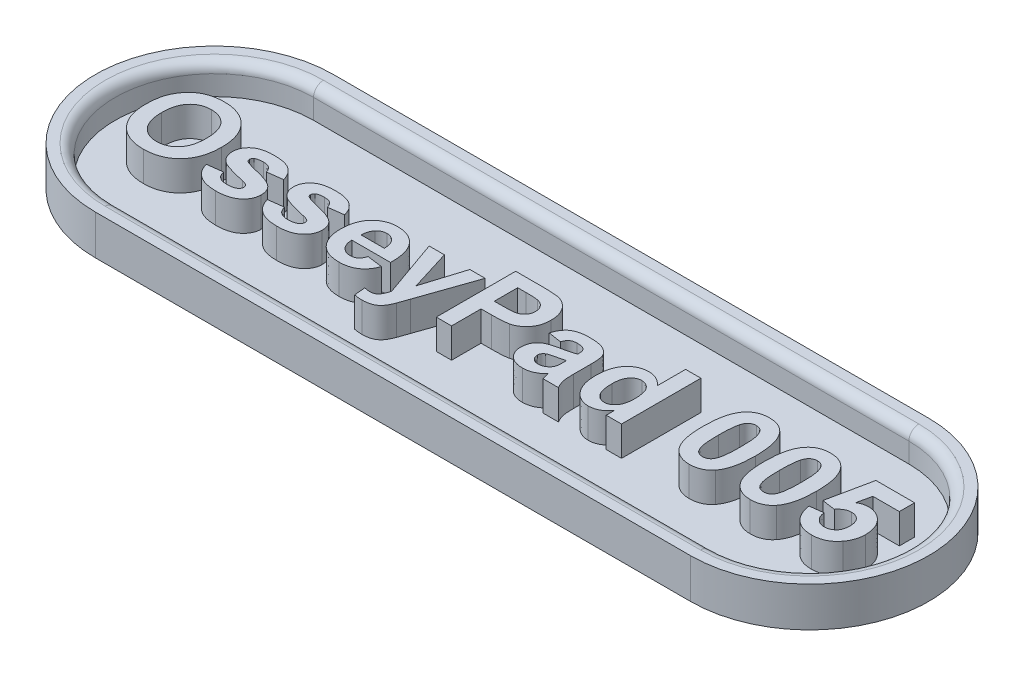
SolidWorks part; units mm, degrees
ref_plane "Front Plane" through (0, 0, 0) normal (0, 0, 1) x (1, 0, 0)
ref_plane "Top Plane" through (0, 0, 0) normal (0, 1, 0) x (1, 0, 0)
ref_plane "Right Plane" through (0, 0, 0) normal (1, 0, 0) x (0, 0, -1)
sketch "Sketch1" plane through (0, 0, 0) normal (0, 1, 0) x (1, 0, 0)
  line L0 (-15, 0) -> (15, 0) construction
  line L1 (-15, 6) -> (15, 6)
  line L2 (-15, -6) -> (15, -6)
  arc A0 (-15, 6) -> (-15, -6) centre (-15, 0) ccw
  arc A1 (15, -6) -> (15, 6) centre (15, 0) ccw
  point P2 (0, 0)
  dimension "D1" = 12
  dimension "D2" = 30
extrude "Boss-Extrude1" add sketch "Sketch1" along normal blind 2
sketch "Sketch2" plane through (0, 2, 0) normal (0, 1, 0) x (1, 0, 0)
  line L0 (-15, 0) -> (15, 0) construction
  line L1 (-15, 5) -> (15, 5)
  line L2 (-15, -5) -> (15, -5)
  arc A0 (-15, 5) -> (-15, -5) centre (-15, 0) ccw
  arc A1 (15, -5) -> (15, 5) centre (15, 0) ccw
  point P2 (0, 0)
  dimension "D1" = 30
  dimension "D2" = 10
extrude "Cut-Extrude1" cut sketch "Sketch2" against normal blind 1.5
sketch "Sketch3" plane through (0, 0.5, 0) normal (0, 1, 0) x (1, 0, 0)
  line L0 (-21, -1.995) -> (21, -1.995) construction
  line L1 (0, -8.7006) -> (0, 6.9821) construction
  line L3 (-15, -5) -> (15, -5) construction
  text T0 "OsseyPad 005" font "Arial" height 4
  dimension "D1" = 3.005
extrude "Boss-Extrude2" add sketch "Sketch3" along normal blind 1.5
fillet "Fillet1" radius 0.5 4 edges at (0, 2, -5) (20, 2, 0) (0, 2, 5) (-20, 2, 0)
